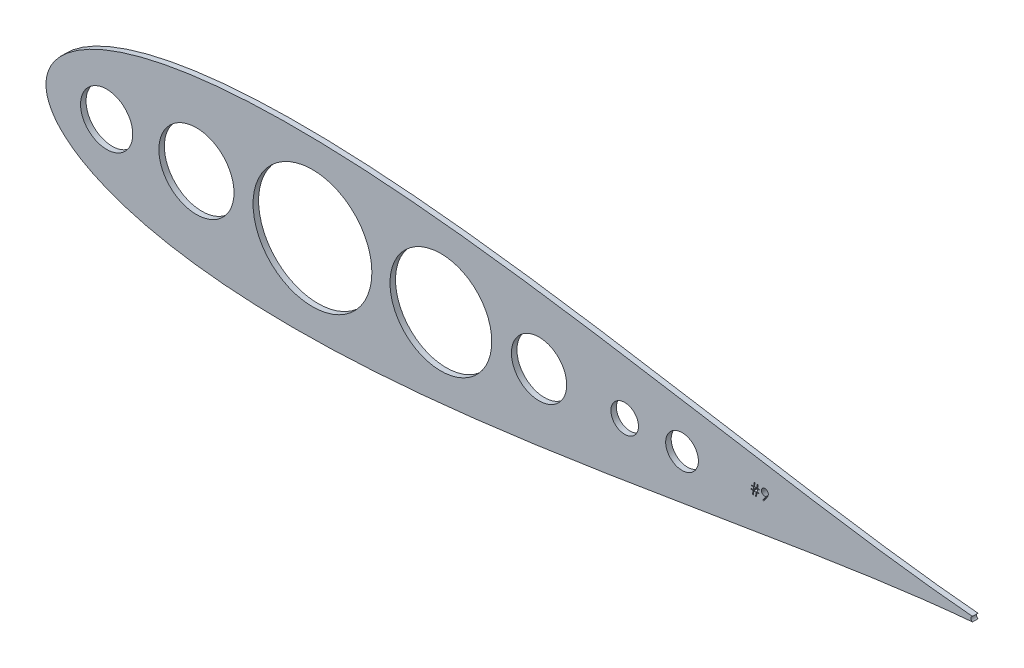
SolidWorks part; units mm, degrees
ref_plane "Front Plane" through (0, 0, 0) normal (0, 0, 1) x (1, 0, 0)
ref_plane "Top Plane" through (0, 0, 0) normal (0, 1, 0) x (1, 0, 0)
ref_plane "Right Plane" through (0, 0, 0) normal (1, 0, 0) x (0, 0, -1)
sketch "Model" plane through (0, 0, 0) normal (0, 0, 1) x (1, 0, 0)
  line L0 (623.2863, 563.4116) -> (623.2863, 563.0859)
  line L1 (623.2863, 563.0859) -> (622.3155, 563.0859)
  line L2 (622.3155, 563.0859) -> (622.0519, 561.3275)
  line L3 (622.0519, 561.3275) -> (621.6581, 561.3275)
  line L4 (621.6581, 561.3275) -> (621.9217, 563.0859)
  line L5 (621.9217, 563.0859) -> (620.8827, 563.0859)
  line L6 (620.8827, 563.0859) -> (620.6191, 561.3275)
  line L7 (620.6191, 561.3275) -> (620.2253, 561.3275)
  line L8 (620.2253, 561.3275) -> (620.4888, 563.0859)
  line L9 (620.4888, 563.0859) -> (619.6391, 563.0859)
  line L10 (619.6391, 563.0859) -> (619.6391, 563.4116)
  line L11 (619.6391, 563.4116) -> (620.5377, 563.4116)
  line L12 (620.5377, 563.4116) -> (620.7137, 564.5839)
  line L13 (620.7137, 564.5839) -> (619.7694, 564.5839)
  line L14 (619.7694, 564.5839) -> (619.7694, 564.9095)
  line L15 (619.7694, 564.9095) -> (620.7626, 564.9095)
  line L16 (620.7626, 564.9095) -> (621.0068, 566.5377)
  line L17 (621.0068, 566.5377) -> (621.3996, 566.5377)
  line L18 (621.3996, 566.5377) -> (621.1554, 564.9095)
  line L19 (621.1554, 564.9095) -> (622.1954, 564.9095)
  line L20 (622.1954, 564.9095) -> (622.4396, 566.5377)
  line L21 (622.4396, 566.5377) -> (622.8324, 566.5377)
  line L22 (622.8324, 566.5377) -> (622.5882, 564.9095)
  line L23 (622.5882, 564.9095) -> (623.4166, 564.9095)
  line L24 (623.4166, 564.9095) -> (623.4166, 564.5839)
  line L25 (623.4166, 564.5839) -> (622.5394, 564.5839)
  line L26 (622.5394, 564.5839) -> (622.3643, 563.4116)
  line L27 (622.3643, 563.4116) -> (623.2863, 563.4116)
  line L28 (622.1466, 564.5839) -> (621.1065, 564.5839)
  line L29 (621.1065, 564.5839) -> (620.9315, 563.4116)
  line L30 (620.9315, 563.4116) -> (621.9705, 563.4116)
  line L31 (621.9705, 563.4116) -> (622.1466, 564.5839)
  line L32 (625.3704, 561.1972) -> (625.0061, 561.4506)
  line L33 (625.0061, 561.4506) -> (626.4186, 563.5154)
  line L34 (626.4186, 563.5154) -> (626.1479, 563.4869)
  line L35 (626.1479, 563.4869) -> (625.8843, 563.4767)
  line L36 (625.8843, 563.4767) -> (625.7245, 563.4838)
  line L37 (625.7245, 563.4838) -> (625.5719, 563.5042)
  line L38 (625.5719, 563.5042) -> (625.4243, 563.5378)
  line L39 (625.4243, 563.5378) -> (625.2839, 563.5856)
  line L40 (625.2839, 563.5856) -> (625.1486, 563.6466)
  line L41 (625.1486, 563.6466) -> (625.0203, 563.7209)
  line L42 (625.0203, 563.7209) -> (624.8972, 563.8095)
  line L43 (624.8972, 563.8095) -> (624.7812, 563.9112)
  line L44 (624.7812, 563.9112) -> (624.6754, 564.0232)
  line L45 (624.6754, 564.0232) -> (624.5828, 564.1412)
  line L46 (624.5828, 564.1412) -> (624.5054, 564.2654)
  line L47 (624.5054, 564.2654) -> (624.4413, 564.3966)
  line L48 (624.4413, 564.3966) -> (624.3925, 564.533)
  line L49 (624.3925, 564.533) -> (624.3568, 564.6765)
  line L50 (624.3568, 564.6765) -> (624.3355, 564.8261)
  line L51 (624.3355, 564.8261) -> (624.3284, 564.9818)
  line L52 (624.3284, 564.9818) -> (624.3416, 565.1945)
  line L53 (624.3416, 565.1945) -> (624.3803, 565.3959)
  line L54 (624.3803, 565.3959) -> (624.4454, 565.5873)
  line L55 (624.4454, 565.5873) -> (624.5359, 565.7674)
  line L56 (624.5359, 565.7674) -> (624.6509, 565.9343)
  line L57 (624.6509, 565.9343) -> (624.7873, 566.0828)
  line L58 (624.7873, 566.0828) -> (624.9461, 566.2141)
  line L59 (624.9461, 566.2141) -> (625.1262, 566.3281)
  line L60 (625.1262, 566.3281) -> (625.3205, 566.4197)
  line L61 (625.3205, 566.4197) -> (625.522, 566.4858)
  line L62 (625.522, 566.4858) -> (625.7306, 566.5245)
  line L63 (625.7306, 566.5245) -> (625.9454, 566.5377)
  line L64 (625.9454, 566.5377) -> (626.156, 566.5245)
  line L65 (626.156, 566.5245) -> (626.3585, 566.4868)
  line L66 (626.3585, 566.4868) -> (626.5529, 566.4227)
  line L67 (626.5529, 566.4227) -> (626.7391, 566.3332)
  line L68 (626.7391, 566.3332) -> (626.9121, 566.2202)
  line L69 (626.9121, 566.2202) -> (627.0648, 566.0879)
  line L70 (627.0648, 566.0879) -> (627.1981, 565.9343)
  line L71 (627.1981, 565.9343) -> (627.312, 565.7603)
  line L72 (627.312, 565.7603) -> (627.4026, 565.574)
  line L73 (627.4026, 565.574) -> (627.4677, 565.3807)
  line L74 (627.4677, 565.3807) -> (627.5064, 565.1822)
  line L75 (627.5064, 565.1822) -> (627.5196, 564.9767)
  line L76 (627.5196, 564.9767) -> (627.5115, 564.8169)
  line L77 (627.5115, 564.8169) -> (627.4881, 564.6541)
  line L78 (627.4881, 564.6541) -> (627.4474, 564.4862)
  line L79 (627.4474, 564.4862) -> (627.3914, 564.3152)
  line L80 (627.3914, 564.3152) -> (627.3568, 564.2267)
  line L81 (627.3568, 564.2267) -> (627.3151, 564.1341)
  line L82 (627.3151, 564.1341) -> (627.2673, 564.0364)
  line L83 (627.2673, 564.0364) -> (627.2133, 563.9356)
  line L84 (627.2133, 563.9356) -> (627.1533, 563.8288)
  line L85 (627.1533, 563.8288) -> (627.0871, 563.7189)
  line L86 (627.0871, 563.7189) -> (627.0139, 563.6039)
  line L87 (627.0139, 563.6039) -> (626.9345, 563.4848)
  line L88 (626.9345, 563.4848) -> (625.3704, 561.1972)
  line L89 (625.9688, 563.9977) -> (626.0899, 564.0028)
  line L90 (626.0899, 564.0028) -> (626.2038, 564.016)
  line L91 (626.2038, 564.016) -> (626.3127, 564.0394)
  line L92 (626.3127, 564.0394) -> (626.4145, 564.072)
  line L93 (626.4145, 564.072) -> (626.5112, 564.1127)
  line L94 (626.5112, 564.1127) -> (626.6017, 564.1636)
  line L95 (626.6017, 564.1636) -> (626.6852, 564.2236)
  line L96 (626.6852, 564.2236) -> (626.7635, 564.2928)
  line L97 (626.7635, 564.2928) -> (626.8338, 564.3692)
  line L98 (626.8338, 564.3692) -> (626.8948, 564.4485)
  line L99 (626.8948, 564.4485) -> (626.9467, 564.532)
  line L100 (626.9467, 564.532) -> (626.9884, 564.6195)
  line L101 (626.9884, 564.6195) -> (627.022, 564.7111)
  line L102 (627.022, 564.7111) -> (627.0454, 564.8057)
  line L103 (627.0454, 564.8057) -> (627.0586, 564.9044)
  line L104 (627.0586, 564.9044) -> (627.0637, 565.0072)
  line L105 (627.0637, 565.0072) -> (627.0586, 565.11)
  line L106 (627.0586, 565.11) -> (627.0434, 565.2087)
  line L107 (627.0434, 565.2087) -> (627.0169, 565.3033)
  line L108 (627.0169, 565.3033) -> (626.9803, 565.3949)
  line L109 (626.9803, 565.3949) -> (626.9335, 565.4814)
  line L110 (626.9335, 565.4814) -> (626.8765, 565.5649)
  line L111 (626.8765, 565.5649) -> (626.8083, 565.6453)
  line L112 (626.8083, 565.6453) -> (626.73, 565.7206)
  line L113 (626.73, 565.7206) -> (626.6445, 565.7898)
  line L114 (626.6445, 565.7898) -> (626.5549, 565.8498)
  line L115 (626.5549, 565.8498) -> (626.4603, 565.9007)
  line L116 (626.4603, 565.9007) -> (626.3616, 565.9424)
  line L117 (626.3616, 565.9424) -> (626.2588, 565.975)
  line L118 (626.2588, 565.975) -> (626.1509, 565.9984)
  line L119 (626.1509, 565.9984) -> (626.039, 566.0116)
  line L120 (626.039, 566.0116) -> (625.922, 566.0167)
  line L121 (625.922, 566.0167) -> (625.8059, 566.0116)
  line L122 (625.8059, 566.0116) -> (625.695, 565.9984)
  line L123 (625.695, 565.9984) -> (625.5882, 565.975)
  line L124 (625.5882, 565.975) -> (625.4854, 565.9424)
  line L125 (625.4854, 565.9424) -> (625.3867, 565.9007)
  line L126 (625.3867, 565.9007) -> (625.292, 565.8498)
  line L127 (625.292, 565.8498) -> (625.2025, 565.7898)
  line L128 (625.2025, 565.7898) -> (625.117, 565.7206)
  line L129 (625.117, 565.7206) -> (625.0387, 565.6453)
  line L130 (625.0387, 565.6453) -> (624.9715, 565.5649)
  line L131 (624.9715, 565.5649) -> (624.9145, 565.4814)
  line L132 (624.9145, 565.4814) -> (624.8677, 565.3949)
  line L133 (624.8677, 565.3949) -> (624.8311, 565.3033)
  line L134 (624.8311, 565.3033) -> (624.8046, 565.2087)
  line L135 (624.8046, 565.2087) -> (624.7893, 565.11)
  line L136 (624.7893, 565.11) -> (624.7842, 565.0072)
  line L137 (624.7842, 565.0072) -> (624.7893, 564.9044)
  line L138 (624.7893, 564.9044) -> (624.8056, 564.8057)
  line L139 (624.8056, 564.8057) -> (624.8331, 564.7111)
  line L140 (624.8331, 564.7111) -> (624.8707, 564.6195)
  line L141 (624.8707, 564.6195) -> (624.9196, 564.532)
  line L142 (624.9196, 564.532) -> (624.9796, 564.4485)
  line L143 (624.9796, 564.4485) -> (625.0498, 564.3692)
  line L144 (625.0498, 564.3692) -> (625.1313, 564.2928)
  line L145 (625.1313, 564.2928) -> (625.2198, 564.2236)
  line L146 (625.2198, 564.2236) -> (625.3134, 564.1636)
  line L147 (625.3134, 564.1636) -> (625.4121, 564.1127)
  line L148 (625.4121, 564.1127) -> (625.5139, 564.072)
  line L149 (625.5139, 564.072) -> (625.6207, 564.0394)
  line L150 (625.6207, 564.0394) -> (625.7327, 564.016)
  line L151 (625.7327, 564.016) -> (625.8487, 564.0028)
  line L152 (625.8487, 564.0028) -> (625.9688, 563.9977)
  circle A0 centre (323.3609, 562.2205) radius 12.0033
  circle A1 centre (364.6359, 562.2205) radius 17.272
  circle A2 centre (417.9739, 562.2205) radius 27.3042
  circle A3 centre (522.1159, 562.2205) radius 12.7
  circle A4 centre (587.8499, 562.2205) radius 7.5268
  circle A5 centre (476.9933, 562.2205) radius 23.3878
  arc A6 (721.3547, 563.3347) -> (721.3547, 561.1062) centre (721.9092, 562.2205) ccw
  circle A7 centre (561.4859, 562.2205) radius 6.35
  spline S0 degree 3 poles (721.3547, 563.3347) (720.6697, 563.3937) (719.2831, 563.5129) (717.1795, 563.7049) (715.027, 563.909) (712.8258, 564.1261) (710.5758, 564.3559) (706.8162, 564.7527) (701.4517, 565.3535) (694.6116, 566.178) (687.6695, 567.0662) (678.4974, 568.2993) (666.9946, 569.9442) (653.2696, 572.0254) (639.558, 574.1929) (625.856, 576.4204) (614.4427, 578.307) (605.3133, 579.8236) (596.1841, 581.3417) (584.772, 583.2355) (571.0732, 585.482) (557.3669, 587.6825) (543.6501, 589.8171) (525.3436, 592.5482) (502.421, 595.6945) (474.8362, 598.859) (451.668, 600.8188) (433.1853, 601.8272) (419.1871, 602.2705) (405.4133, 602.3433) (391.3853, 601.986) (377.6479, 601.1387) (363.8386, 599.6826) (352.552, 597.8958) (343.4942, 595.9879) (336.6896, 594.2763) (330.04, 592.2734) (323.5087, 589.9111) (317.2099, 587.1559) (311.098, 583.8457) (306.3002, 580.5092) (302.8358, 577.43) (300.4444, 574.85) (298.4146, 572.067) (296.7932, 568.9812) (295.737, 565.6945) (295.362, 562.2205) (295.737, 558.7464) (296.7932, 555.4599) (298.4145, 552.3741) (300.4442, 549.5912) (302.8356, 547.0111) (306.3001, 543.9319) (311.098, 540.5953) (317.2099, 537.2851) (323.5086, 534.5299) (330.0398, 532.1677) (336.6894, 530.1647) (343.4942, 528.4531) (352.552, 526.5452) (363.8384, 524.7584) (377.6477, 523.3023) (391.3849, 522.455) (405.4132, 522.0977) (419.1867, 522.1705) (433.1852, 522.6138) (451.6678, 523.6221) (474.8362, 525.582) (502.421, 528.7465) (525.3436, 531.8927) (543.6501, 534.6238) (557.3669, 536.7585) (571.0732, 538.959) (584.772, 541.2055) (596.1841, 543.0993) (605.3133, 544.6174) (614.4427, 546.134) (625.856, 548.0206) (639.558, 550.2481) (653.2696, 552.4155) (666.9946, 554.4967) (678.4973, 556.1417) (687.6694, 557.3747) (694.6113, 558.2629) (701.4516, 559.0874) (707.5652, 559.7723) (712.7758, 560.3133) (717.1293, 560.7373) (719.9683, 560.9852) (721.3547, 561.1062) knots 0 0 0 0 0.002326 0.004707 0.007145 0.009639 0.012189 0.014795 0.022426 0.030447 0.038099 0.046099 0.06175 0.077401 0.093053 0.108704 0.124356 0.132182 0.140007 0.155659 0.17131 0.186962 0.202613 0.218265 0.249567 0.28087 0.312172 0.328195 0.343475 0.359539 0.374777 0.390931 0.40608 0.421731 0.429557 0.437383 0.445457 0.453036 0.460863 0.46869 0.476515 0.480564 0.484347 0.488394 0.492178 0.496091 0.5 0.503909 0.507822 0.511605 0.515653 0.519435 0.523485 0.53131 0.539137 0.546964 0.554542 0.562617 0.570443 0.578269 0.59392 0.609068 0.625223 0.64046 0.656525 0.671805 0.687828 0.71913 0.750433 0.781735 0.797387 0.813038 0.82869 0.844341 0.859993 0.867818 0.875644 0.891296 0.906947 0.922599 0.93825 0.953901 0.961901 0.969553 0.977573 0.985205 0.990361 0.995293 1 1 1 1
sketch "Sketch2" plane through (0, 0, 0) normal (0, 0, 1) x (1, 0, 0)
  line L0 (623.2863, 563.4116) -> (623.2863, 563.0859)
  line L1 (623.2863, 563.0859) -> (622.3155, 563.0859)
  line L2 (622.3155, 563.0859) -> (622.0519, 561.3275)
  line L3 (622.0519, 561.3275) -> (621.6581, 561.3275)
  line L4 (621.6581, 561.3275) -> (621.9217, 563.0859)
  line L5 (621.9217, 563.0859) -> (620.8827, 563.0859)
  line L6 (620.8827, 563.0859) -> (620.6191, 561.3275)
  line L7 (620.6191, 561.3275) -> (620.2253, 561.3275)
  line L8 (620.2253, 561.3275) -> (620.4888, 563.0859)
  line L9 (620.4888, 563.0859) -> (619.6391, 563.0859)
  line L10 (619.6391, 563.0859) -> (619.6391, 563.4116)
  line L11 (619.6391, 563.4116) -> (620.5377, 563.4116)
  line L12 (620.5377, 563.4116) -> (620.7137, 564.5839)
  line L13 (620.7137, 564.5839) -> (619.7694, 564.5839)
  line L14 (619.7694, 564.5839) -> (619.7694, 564.9095)
  line L15 (619.7694, 564.9095) -> (620.7626, 564.9095)
  line L16 (620.7626, 564.9095) -> (621.0068, 566.5377)
  line L17 (621.0068, 566.5377) -> (621.3996, 566.5377)
  line L18 (621.3996, 566.5377) -> (621.1554, 564.9095)
  line L19 (621.1554, 564.9095) -> (622.1954, 564.9095)
  line L20 (622.1954, 564.9095) -> (622.4396, 566.5377)
  line L21 (622.4396, 566.5377) -> (622.8324, 566.5377)
  line L22 (622.8324, 566.5377) -> (622.5882, 564.9095)
  line L23 (622.5882, 564.9095) -> (623.4166, 564.9095)
  line L24 (623.4166, 564.9095) -> (623.4166, 564.5839)
  line L25 (623.4166, 564.5839) -> (622.5394, 564.5839)
  line L26 (622.5394, 564.5839) -> (622.3643, 563.4116)
  line L27 (622.3643, 563.4116) -> (623.2863, 563.4116)
  line L28 (622.1466, 564.5839) -> (621.1065, 564.5839)
  line L29 (621.1065, 564.5839) -> (620.9315, 563.4116)
  line L30 (620.9315, 563.4116) -> (621.9705, 563.4116)
  line L31 (621.9705, 563.4116) -> (622.1466, 564.5839)
  line L32 (625.3704, 561.1972) -> (625.0061, 561.4506)
  line L33 (625.0061, 561.4506) -> (626.4186, 563.5154)
  line L34 (626.4186, 563.5154) -> (626.1479, 563.4869)
  line L35 (626.1479, 563.4869) -> (625.8843, 563.4767)
  line L36 (625.8843, 563.4767) -> (625.7245, 563.4838)
  line L37 (625.7245, 563.4838) -> (625.5719, 563.5042)
  line L38 (625.5719, 563.5042) -> (625.4243, 563.5378)
  line L39 (625.4243, 563.5378) -> (625.2839, 563.5856)
  line L40 (625.2839, 563.5856) -> (625.1486, 563.6466)
  line L41 (625.1486, 563.6466) -> (625.0203, 563.7209)
  line L42 (625.0203, 563.7209) -> (624.8972, 563.8095)
  line L43 (624.8972, 563.8095) -> (624.7812, 563.9112)
  line L44 (624.7812, 563.9112) -> (624.6754, 564.0232)
  line L45 (624.6754, 564.0232) -> (624.5828, 564.1412)
  line L46 (624.5828, 564.1412) -> (624.5054, 564.2654)
  line L47 (624.5054, 564.2654) -> (624.4413, 564.3966)
  line L48 (624.4413, 564.3966) -> (624.3925, 564.533)
  line L49 (624.3925, 564.533) -> (624.3568, 564.6765)
  line L50 (624.3568, 564.6765) -> (624.3355, 564.8261)
  line L51 (624.3355, 564.8261) -> (624.3284, 564.9818)
  line L52 (624.3284, 564.9818) -> (624.3416, 565.1945)
  line L53 (624.3416, 565.1945) -> (624.3803, 565.3959)
  line L54 (624.3803, 565.3959) -> (624.4454, 565.5873)
  line L55 (624.4454, 565.5873) -> (624.5359, 565.7674)
  line L56 (624.5359, 565.7674) -> (624.6509, 565.9343)
  line L57 (624.6509, 565.9343) -> (624.7873, 566.0828)
  line L58 (624.7873, 566.0828) -> (624.9461, 566.2141)
  line L59 (624.9461, 566.2141) -> (625.1262, 566.3281)
  line L60 (625.1262, 566.3281) -> (625.3205, 566.4197)
  line L61 (625.3205, 566.4197) -> (625.522, 566.4858)
  line L62 (625.522, 566.4858) -> (625.7306, 566.5245)
  line L63 (625.7306, 566.5245) -> (625.9454, 566.5377)
  line L64 (625.9454, 566.5377) -> (626.156, 566.5245)
  line L65 (626.156, 566.5245) -> (626.3585, 566.4868)
  line L66 (626.3585, 566.4868) -> (626.5529, 566.4227)
  line L67 (626.5529, 566.4227) -> (626.7391, 566.3332)
  line L68 (626.7391, 566.3332) -> (626.9121, 566.2202)
  line L69 (626.9121, 566.2202) -> (627.0648, 566.0879)
  line L70 (627.0648, 566.0879) -> (627.1981, 565.9343)
  line L71 (627.1981, 565.9343) -> (627.312, 565.7603)
  line L72 (627.312, 565.7603) -> (627.4026, 565.574)
  line L73 (627.4026, 565.574) -> (627.4677, 565.3807)
  line L74 (627.4677, 565.3807) -> (627.5064, 565.1822)
  line L75 (627.5064, 565.1822) -> (627.5196, 564.9767)
  line L76 (627.5196, 564.9767) -> (627.5115, 564.8169)
  line L77 (627.5115, 564.8169) -> (627.4881, 564.6541)
  line L78 (627.4881, 564.6541) -> (627.4474, 564.4862)
  line L79 (627.4474, 564.4862) -> (627.3914, 564.3152)
  line L80 (627.3914, 564.3152) -> (627.3568, 564.2267)
  line L81 (627.3568, 564.2267) -> (627.3151, 564.1341)
  line L82 (627.3151, 564.1341) -> (627.2673, 564.0364)
  line L83 (627.2673, 564.0364) -> (627.2133, 563.9356)
  line L84 (627.2133, 563.9356) -> (627.1533, 563.8288)
  line L85 (627.1533, 563.8288) -> (627.0871, 563.7189)
  line L86 (627.0871, 563.7189) -> (627.0139, 563.6039)
  line L87 (627.0139, 563.6039) -> (626.9345, 563.4848)
  line L88 (626.9345, 563.4848) -> (625.3704, 561.1972)
  line L89 (625.9688, 563.9977) -> (626.0899, 564.0028)
  line L90 (626.0899, 564.0028) -> (626.2038, 564.016)
  line L91 (626.2038, 564.016) -> (626.3127, 564.0394)
  line L92 (626.3127, 564.0394) -> (626.4145, 564.072)
  line L93 (626.4145, 564.072) -> (626.5112, 564.1127)
  line L94 (626.5112, 564.1127) -> (626.6017, 564.1636)
  line L95 (626.6017, 564.1636) -> (626.6852, 564.2236)
  line L96 (626.6852, 564.2236) -> (626.7635, 564.2928)
  line L97 (626.7635, 564.2928) -> (626.8338, 564.3692)
  line L98 (626.8338, 564.3692) -> (626.8948, 564.4485)
  line L99 (626.8948, 564.4485) -> (626.9467, 564.532)
  line L100 (626.9467, 564.532) -> (626.9884, 564.6195)
  line L101 (626.9884, 564.6195) -> (627.022, 564.7111)
  line L102 (627.022, 564.7111) -> (627.0454, 564.8057)
  line L103 (627.0454, 564.8057) -> (627.0586, 564.9044)
  line L104 (627.0586, 564.9044) -> (627.0637, 565.0072)
  line L105 (627.0637, 565.0072) -> (627.0586, 565.11)
  line L106 (627.0586, 565.11) -> (627.0434, 565.2087)
  line L107 (627.0434, 565.2087) -> (627.0169, 565.3033)
  line L108 (627.0169, 565.3033) -> (626.9803, 565.3949)
  line L109 (626.9803, 565.3949) -> (626.9335, 565.4814)
  line L110 (626.9335, 565.4814) -> (626.8765, 565.5649)
  line L111 (626.8765, 565.5649) -> (626.8083, 565.6453)
  line L112 (626.8083, 565.6453) -> (626.73, 565.7206)
  line L113 (626.73, 565.7206) -> (626.6445, 565.7898)
  line L114 (626.6445, 565.7898) -> (626.5549, 565.8498)
  line L115 (626.5549, 565.8498) -> (626.4603, 565.9007)
  line L116 (626.4603, 565.9007) -> (626.3616, 565.9424)
  line L117 (626.3616, 565.9424) -> (626.2588, 565.975)
  line L118 (626.2588, 565.975) -> (626.1509, 565.9984)
  line L119 (626.1509, 565.9984) -> (626.039, 566.0116)
  line L120 (626.039, 566.0116) -> (625.922, 566.0167)
  line L121 (625.922, 566.0167) -> (625.8059, 566.0116)
  line L122 (625.8059, 566.0116) -> (625.695, 565.9984)
  line L123 (625.695, 565.9984) -> (625.5882, 565.975)
  line L124 (625.5882, 565.975) -> (625.4854, 565.9424)
  line L125 (625.4854, 565.9424) -> (625.3867, 565.9007)
  line L126 (625.3867, 565.9007) -> (625.292, 565.8498)
  line L127 (625.292, 565.8498) -> (625.2025, 565.7898)
  line L128 (625.2025, 565.7898) -> (625.117, 565.7206)
  line L129 (625.117, 565.7206) -> (625.0387, 565.6453)
  line L130 (625.0387, 565.6453) -> (624.9715, 565.5649)
  line L131 (624.9715, 565.5649) -> (624.9145, 565.4814)
  line L132 (624.9145, 565.4814) -> (624.8677, 565.3949)
  line L133 (624.8677, 565.3949) -> (624.8311, 565.3033)
  line L134 (624.8311, 565.3033) -> (624.8046, 565.2087)
  line L135 (624.8046, 565.2087) -> (624.7893, 565.11)
  line L136 (624.7893, 565.11) -> (624.7842, 565.0072)
  line L137 (624.7842, 565.0072) -> (624.7893, 564.9044)
  line L138 (624.7893, 564.9044) -> (624.8056, 564.8057)
  line L139 (624.8056, 564.8057) -> (624.8331, 564.7111)
  line L140 (624.8331, 564.7111) -> (624.8707, 564.6195)
  line L141 (624.8707, 564.6195) -> (624.9196, 564.532)
  line L142 (624.9196, 564.532) -> (624.9796, 564.4485)
  line L143 (624.9796, 564.4485) -> (625.0498, 564.3692)
  line L144 (625.0498, 564.3692) -> (625.1313, 564.2928)
  line L145 (625.1313, 564.2928) -> (625.2198, 564.2236)
  line L146 (625.2198, 564.2236) -> (625.3134, 564.1636)
  line L147 (625.3134, 564.1636) -> (625.4121, 564.1127)
  line L148 (625.4121, 564.1127) -> (625.5139, 564.072)
  line L149 (625.5139, 564.072) -> (625.6207, 564.0394)
  line L150 (625.6207, 564.0394) -> (625.7327, 564.016)
  line L151 (625.7327, 564.016) -> (625.8487, 564.0028)
  line L152 (625.8487, 564.0028) -> (625.9688, 563.9977)
  circle A0 centre (323.3609, 562.2205) radius 12.0033
  circle A1 centre (364.6359, 562.2205) radius 17.272
  circle A2 centre (417.9739, 562.2205) radius 27.3042
  circle A3 centre (522.1159, 562.2205) radius 12.7
  circle A4 centre (587.8499, 562.2205) radius 7.5268
  circle A5 centre (476.9933, 562.2205) radius 23.3878
  arc A6 (721.3547, 563.3347) -> (721.3547, 561.1062) centre (721.9092, 562.2205) ccw
  circle A7 centre (561.4859, 562.2205) radius 6.35
  spline S0 degree 3 poles (721.3547, 563.3347) (720.6697, 563.3937) (719.2831, 563.5129) (717.1795, 563.7049) (715.027, 563.909) (712.8258, 564.1261) (710.5758, 564.3559) (706.8162, 564.7527) (701.4517, 565.3535) (694.6116, 566.178) (687.6695, 567.0662) (678.4974, 568.2993) (666.9946, 569.9442) (653.2696, 572.0254) (639.558, 574.1929) (625.856, 576.4204) (614.4427, 578.307) (605.3133, 579.8236) (596.1841, 581.3417) (584.772, 583.2355) (571.0732, 585.482) (557.3669, 587.6825) (543.6501, 589.8171) (525.3436, 592.5482) (502.421, 595.6945) (474.8362, 598.859) (451.668, 600.8188) (433.1853, 601.8272) (419.1871, 602.2705) (405.4133, 602.3433) (391.3853, 601.986) (377.6479, 601.1387) (363.8386, 599.6826) (352.552, 597.8958) (343.4942, 595.9879) (336.6896, 594.2763) (330.04, 592.2734) (323.5087, 589.9111) (317.2099, 587.1559) (311.098, 583.8457) (306.3002, 580.5092) (302.8358, 577.43) (300.4444, 574.85) (298.4146, 572.067) (296.7932, 568.9812) (295.737, 565.6945) (295.362, 562.2205) (295.737, 558.7464) (296.7932, 555.4599) (298.4145, 552.3741) (300.4442, 549.5912) (302.8356, 547.0111) (306.3001, 543.9319) (311.098, 540.5953) (317.2099, 537.2851) (323.5086, 534.5299) (330.0398, 532.1677) (336.6894, 530.1647) (343.4942, 528.4531) (352.552, 526.5452) (363.8384, 524.7584) (377.6477, 523.3023) (391.3849, 522.455) (405.4132, 522.0977) (419.1867, 522.1705) (433.1852, 522.6138) (451.6678, 523.6221) (474.8362, 525.582) (502.421, 528.7465) (525.3436, 531.8927) (543.6501, 534.6238) (557.3669, 536.7585) (571.0732, 538.959) (584.772, 541.2055) (596.1841, 543.0993) (605.3133, 544.6174) (614.4427, 546.134) (625.856, 548.0206) (639.558, 550.2481) (653.2696, 552.4155) (666.9946, 554.4967) (678.4973, 556.1417) (687.6694, 557.3747) (694.6113, 558.2629) (701.4516, 559.0874) (707.5652, 559.7723) (712.7758, 560.3133) (717.1293, 560.7373) (719.9683, 560.9852) (721.3547, 561.1062) knots 0 0 0 0 0.002326 0.004707 0.007145 0.009639 0.012189 0.014795 0.022426 0.030447 0.038099 0.046099 0.06175 0.077401 0.093053 0.108704 0.124356 0.132182 0.140007 0.155659 0.17131 0.186962 0.202613 0.218265 0.249567 0.28087 0.312172 0.328195 0.343475 0.359539 0.374777 0.390931 0.40608 0.421731 0.429557 0.437383 0.445457 0.453036 0.460863 0.46869 0.476515 0.480564 0.484347 0.488394 0.492178 0.496091 0.5 0.503909 0.507822 0.511605 0.515653 0.519435 0.523485 0.53131 0.539137 0.546964 0.554542 0.562617 0.570443 0.578269 0.59392 0.609068 0.625223 0.64046 0.656525 0.671805 0.687828 0.71913 0.750433 0.781735 0.797387 0.813038 0.82869 0.844341 0.859993 0.867818 0.875644 0.891296 0.906947 0.922599 0.93825 0.953901 0.961901 0.969553 0.977573 0.985205 0.990361 0.995293 1 1 1 1
extrude "Boss-Extrude1" add sketch "Sketch2" along normal blind 2.54 contours A6 S0 L87 L88 L32 L33 L34 L35 L36 L37 L38 L39 L40 L41 L42 L43 L44 L45 L46 L47 L48 L49 L50 L51 L52 L53 L54 L55 L56 L57 L58 L59 L60 L61 L62 L63 L64 L65 L66 L67 L68 L69 L70 L71 L72 L73 L74 L75 L76 L77
